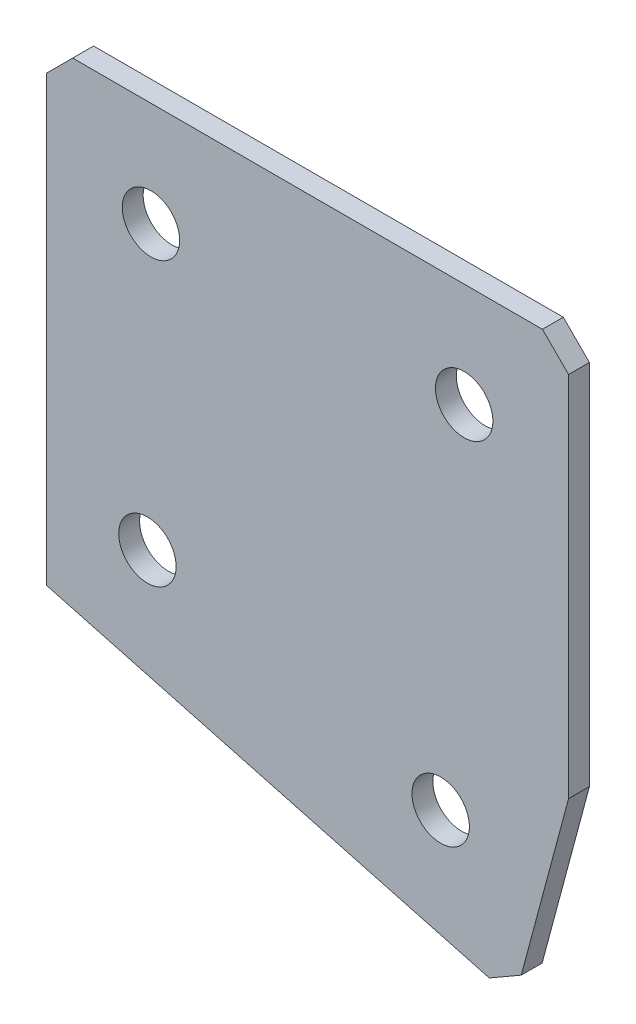
SolidWorks part; units mm, degrees
material "Простая углеродистая сталь"
ref_plane "Спереди" through (0, 0, 0) normal (0, 0, 1) x (1, 0, 0)
ref_plane "Сверху" through (0, 0, 0) normal (0, 1, 0) x (1, 0, 0)
ref_plane "Справа" through (0, 0, 0) normal (1, 0, 0) x (0, 0, -1)
sketch "Эскиз3" plane through (0, 0, 0) normal (0, 0, -1) x (1, 0, 0)
  line L0 (0, 0) -> (50, 0)
  line L1 (50, 0) -> (50, 37.6919)
  line L2 (0, 0) -> (0, 45)
  line L3 (0, 45) -> (44.8236, 57.0105)
  line L4 (44.8236, 57.0105) -> (50, 37.6919)
  dimension "D1" = 50
  dimension "D2" = 45
  dimension "D3" = 20
  dimension "D4" = 15
  dimension "D5" = 37.6919
extrude "Бобышка-Вытянуть1" add sketch "Эскиз3" along normal blind 2
hole_wizard "Отверстие с зазором M51" positions "Эскиз4" profile "Эскиз5" hole size "M5" standard "DIN" end condition through all
sketch "Эскиз4" plane through (0, 0, -2) normal (0, 0, -1) x (1, 0, 0)
  line L0 (9.6593, 37.2354) -> (37.7526, 44.763) construction
  line L2 (44.8236, 57.0105) -> (0, 45) construction
  line L3 (10, 10) -> (40, 10) construction
  line L5 (0, 0) -> (50, 0) construction
  line L6 (0, 45) -> (0, 0) construction
  line L7 (50, 0) -> (50, 37.6919) construction
  line L8 (50, 37.6919) -> (44.8236, 57.0105) construction
  line L9 (9.6593, 37.2354) -> (0, 34.6472) construction
  point P0 (10, 10)
  point P2 (40, 10)
  point P4 (9.6593, 37.2354)
  point P6 (37.7526, 44.763)
  dimension "D1" = 10
  dimension "D2" = 10
  dimension "D3" = 10
  dimension "D4" = 10
  dimension "D5" = 10
  dimension "D6" = 10
  dimension "D7" = 29.0843
  dimension "D8" = 30
sketch "Эскиз5" plane through (10, -10, -2) normal (1, 0, 0) x (0, 1, 0)
  line L0 (0, 0) -> (0, 2)
  line L1 (0, 2) -> (2.75, 2)
  line L2 (2.75, 2) -> (2.75, 0)
  line L5 (2.75, 0) -> (0, 0)
  line L11 (0, -6.35) -> (0, 107.95) construction
  dimension "Диаметр сквозного отверстия" = 5.5
  dimension "Глубина сквозного отверстия" = 2
chamfer "Фаска1" distance 2.5 distance2 2.5 3 edges at (44.8236, -57.0105, -1) (50, 0, -1) (0, 0, -1)
